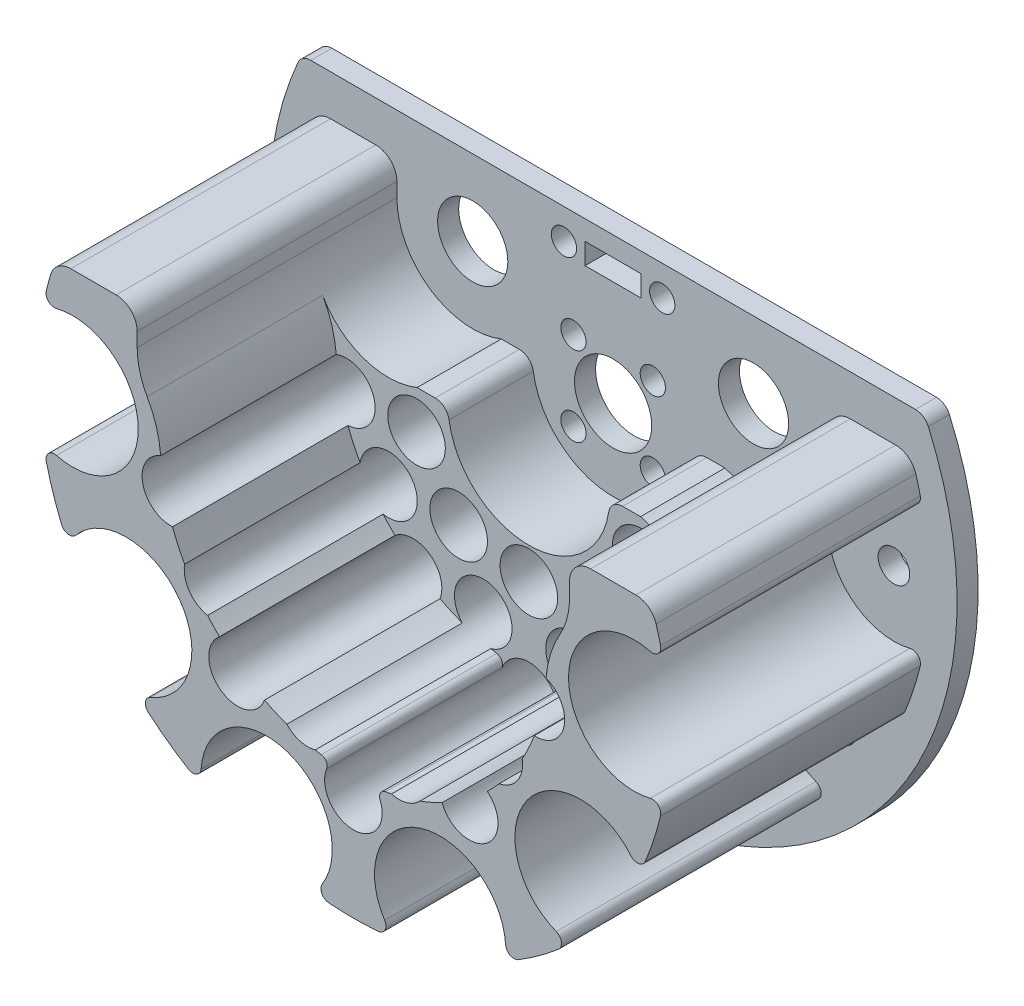
SolidWorks part; units mm, degrees
ref_plane "前视基准面" through (0, 0, 0) normal (0, 0, 1) x (1, 0, 0)
ref_plane "上视基准面" through (0, 0, 0) normal (0, 1, 0) x (1, 0, 0)
ref_plane "右视基准面" through (0, 0, 0) normal (1, 0, 0) x (0, 0, -1)
ref_plane "基准面4" through (0, 0, 40) normal (0, 0, 1) x (1, 0, 0)
sketch "草图1" plane through (0, 0, 40) normal (0, 0, 1) x (1, 0, 0)
  line L0 (-30.8, 160) -> (-30.8, 165)
  line L1 (-30.8, 165) -> (-42.4264, 165)
  line L2 (42.4264, 165) -> (30.8, 165)
  line L3 (30.8, 165) -> (30.8, 160)
  arc A0 (29.3798, 154.6466) -> (27.4312, 148.056) centre (42.4074, 147.2114) ccw
  arc A1 (27.4312, 148.056) -> (-27.4312, 148.056) centre (0, 150) cw
  arc A2 (-27.4312, 148.056) -> (-29.3798, 154.6466) centre (-42.4074, 147.2114) ccw
  arc A3 (-29.3798, 154.6466) -> (-30.8, 160) centre (-20, 160) cw
  arc A4 (-42.4264, 165) -> (-43.756, 160.5075) centre (0, 150) ccw
  arc A5 (-43.756, 160.5075) -> (-42.2947, 159.064) centre (-42.5892, 160.2273) ccw
  arc A6 (-42.2947, 159.064) -> (-42.2947, 140.936) centre (-40, 150) cw
  arc A7 (-42.2947, 140.936) -> (-43.756, 139.4925) centre (-42.5892, 139.7727) ccw
  arc A8 (-43.756, 139.4925) -> (-41.5756, 132.7816) centre (0, 150) ccw
  arc A9 (-41.5756, 132.7816) -> (-39.5448, 132.4728) centre (-40.4669, 133.2408) ccw
  arc A10 (-39.5448, 132.4728) -> (-28.8894, 117.8068) centre (-32.3607, 126.4886) cw
  arc A11 (-28.8894, 117.8068) -> (-29.2232, 115.7801) centre (-28.4439, 116.6926) ccw
  arc A12 (-29.2232, 115.7801) -> (-23.5146, 111.6325) centre (0, 150) ccw
  arc A13 (-23.5146, 111.6325) -> (-21.6902, 112.5763) centre (-22.8876, 112.6557) ccw
  arc A14 (-21.6902, 112.5763) -> (-4.4494, 106.9744) centre (-12.3607, 111.9577) cw
  arc A15 (-4.4494, 106.9744) -> (-3.5281, 105.1385) centre (-3.434, 106.3348) ccw
  arc A16 (-3.5281, 105.1385) -> (3.5281, 105.1385) centre (0, 150) ccw
  arc A17 (3.5281, 105.1385) -> (4.4494, 106.9744) centre (3.434, 106.3348) ccw
  arc A18 (4.4494, 106.9744) -> (21.6902, 112.5763) centre (12.3607, 111.9577) cw
  arc A19 (21.6902, 112.5763) -> (23.5146, 111.6325) centre (22.8876, 112.6557) ccw
  arc A20 (23.5146, 111.6325) -> (29.2232, 115.7801) centre (0, 150) ccw
  arc A21 (29.2232, 115.7801) -> (28.8894, 117.8068) centre (28.4439, 116.6926) ccw
  arc A22 (28.8894, 117.8068) -> (39.5448, 132.4728) centre (32.3607, 126.4886) cw
  arc A23 (39.5448, 132.4728) -> (41.5756, 132.7816) centre (40.4669, 133.2408) ccw
  arc A24 (41.5756, 132.7816) -> (43.756, 139.4925) centre (0, 150) ccw
  arc A25 (43.756, 139.4925) -> (42.2947, 140.936) centre (42.5892, 139.7727) ccw
  arc A26 (42.2947, 140.936) -> (42.2947, 159.064) centre (40, 150) cw
  arc A27 (42.2947, 159.064) -> (43.756, 160.5075) centre (42.5892, 160.2273) ccw
  arc A28 (43.756, 160.5075) -> (42.4264, 165) centre (0, 150) ccw
  arc A29 (30.8, 160) -> (29.3798, 154.6466) centre (20, 160) cw
extrude "凸台-拉伸1" add sketch "草图1" against normal blind 25
sketch "草图2" plane through (0, 0, 15) normal (0, 0, -1) x (-1, 0, 0)
  line L0 (-42.4264, 165) -> (-30.8, 165)
  line L1 (-30.8, 165) -> (-30.8, 160)
  line L2 (-15.9208, 150) -> (-11.5, 150)
  line L3 (11.5, 150) -> (15.9208, 150)
  line L4 (30.8, 160) -> (30.8, 165)
  line L5 (30.8, 165) -> (42.4264, 165)
  arc A0 (-21.6902, 112.5763) -> (-23.5146, 111.6325) centre (-22.8876, 112.6557) cw
  arc A1 (-23.5146, 111.6325) -> (-29.2232, 115.7801) centre (0, 150) cw
  arc A2 (-29.2232, 115.7801) -> (-28.8894, 117.8068) centre (-28.4439, 116.6926) cw
  arc A3 (-28.8894, 117.8068) -> (-39.5448, 132.4728) centre (-32.3607, 126.4886) ccw
  arc A4 (-39.5448, 132.4728) -> (-41.5756, 132.7816) centre (-40.4669, 133.2408) cw
  arc A5 (-41.5756, 132.7816) -> (-43.756, 139.4925) centre (0, 150) cw
  arc A6 (-43.756, 139.4925) -> (-42.2947, 140.936) centre (-42.5892, 139.7727) cw
  arc A7 (-42.2947, 140.936) -> (-42.2947, 159.064) centre (-40, 150) ccw
  arc A8 (-42.2947, 159.064) -> (-43.756, 160.5075) centre (-42.5892, 160.2273) cw
  arc A9 (-43.756, 160.5075) -> (-42.4264, 165) centre (0, 150) cw
  arc A10 (-30.8, 160) -> (-15.9208, 150) centre (-20, 160) ccw
  arc A11 (-11.5, 150) -> (11.5, 150) centre (0, 150) ccw
  arc A12 (15.9208, 150) -> (30.8, 160) centre (20, 160) ccw
  arc A13 (42.4264, 165) -> (43.756, 160.5075) centre (0, 150) cw
  arc A14 (43.756, 160.5075) -> (42.2947, 159.064) centre (42.5892, 160.2273) cw
  arc A15 (42.2947, 159.064) -> (42.2947, 140.936) centre (40, 150) ccw
  arc A16 (42.2947, 140.936) -> (43.756, 139.4925) centre (42.5892, 139.7727) cw
  arc A17 (43.756, 139.4925) -> (41.5756, 132.7816) centre (0, 150) cw
  arc A18 (41.5756, 132.7816) -> (39.5448, 132.4728) centre (40.4669, 133.2408) cw
  arc A19 (39.5448, 132.4728) -> (28.8894, 117.8068) centre (32.3607, 126.4886) ccw
  arc A20 (28.8894, 117.8068) -> (29.2232, 115.7801) centre (28.4439, 116.6926) cw
  arc A21 (29.2232, 115.7801) -> (23.5146, 111.6325) centre (0, 150) cw
  arc A22 (23.5146, 111.6325) -> (21.6902, 112.5763) centre (22.8876, 112.6557) cw
  arc A23 (21.6902, 112.5763) -> (4.4494, 106.9744) centre (12.3607, 111.9577) ccw
  arc A24 (4.4494, 106.9744) -> (3.5281, 105.1385) centre (3.434, 106.3348) cw
  arc A25 (3.5281, 105.1385) -> (-3.5281, 105.1385) centre (0, 150) cw
  arc A26 (-3.5281, 105.1385) -> (-4.4494, 106.9744) centre (-3.434, 106.3348) cw
  arc A27 (-4.4494, 106.9744) -> (-21.6902, 112.5763) centre (-12.3607, 111.9577) ccw
extrude "凸台-拉伸2" add sketch "草图2" along normal blind 12
ref_plane "基准面5" through (0, 0, 3) normal (0, 0, 1) x (1, 0, 0)
sketch "草图3" plane through (0, 0, 3) normal (0, 0, 1) x (1, 0, 0)
  line L0 (44.3662, 170.8) -> (-44.3662, 170.8)
  arc A0 (-44.3662, 170.8) -> (44.3662, 170.8) centre (0, 150) ccw
extrude "凸台-拉伸3" add sketch "草图3" against normal blind 3
sketch "草图4" plane through (0, 0, 0) normal (0, 0, -1) x (-1, 0, 0)
  line L0 (-4, 168) -> (-4, 165)
  line L1 (-4, 165) -> (4, 165)
  line L2 (4, 165) -> (4, 168)
  line L3 (4, 168) -> (-4, 168)
extrude "切除-拉伸1" cut sketch "草图4" against normal through all
ref_plane "基准面6" through (0, 144.5, 0) normal (0, 1, 0) x (1, 0, 0)
sketch "草图5" plane through (0, 144.5, 0) normal (0, 1, 0) x (1, 0, 0)
  line L0 (30.1, -1) -> (26, -1)
  line L1 (26, -1) -> (26, -40)
  line L2 (26, -40) -> (30.1, -40)
  line L3 (30.1, -40) -> (30.1, -1)
  line L4 (26, -1) -> (26, -40) construction
revolve "切除-旋转1" cut sketch "草图5" angle 360 about L4
ref_plane "基准面7" through (0, 136, 0) normal (0, 1, 0) x (1, 0, 0)
sketch "草图6" plane through (0, 136, 0) normal (0, 1, 0) x (1, 0, 0)
  line L0 (24.1, -1) -> (20, -1)
  line L1 (20, -1) -> (20, -40)
  line L2 (20, -40) -> (24.1, -40)
  line L3 (24.1, -40) -> (24.1, -1)
  line L4 (20, -1) -> (20, -40) construction
revolve "切除-旋转2" cut sketch "草图6" angle 360 about L4
ref_plane "基准面8" through (0, 127, 0) normal (0, 1, 0) x (1, 0, 0)
sketch "草图7" plane through (0, 127, 0) normal (0, 1, 0) x (1, 0, 0)
  line L0 (10.6, -1) -> (6.5, -1)
  line L1 (6.5, -1) -> (6.5, -40)
  line L2 (6.5, -40) -> (10.6, -40)
  line L3 (10.6, -40) -> (10.6, -1)
  line L4 (6.5, -1) -> (6.5, -40) construction
revolve "切除-旋转3" cut sketch "草图7" angle 360 about L4
sketch "草图8" plane through (0, 127, 0) normal (0, 1, 0) x (1, 0, 0)
  line L0 (-2.4, -1) -> (-6.5, -1)
  line L1 (-6.5, -1) -> (-6.5, -40)
  line L2 (-6.5, -40) -> (-2.4, -40)
  line L3 (-2.4, -40) -> (-2.4, -1)
  line L4 (-6.5, -1) -> (-6.5, -40) construction
revolve "切除-旋转4" cut sketch "草图8" angle 360 about L4
sketch "草图9" plane through (0, 136, 0) normal (0, 1, 0) x (1, 0, 0)
  line L0 (-15.9, -1) -> (-20, -1)
  line L1 (-20, -1) -> (-20, -40)
  line L2 (-20, -40) -> (-15.9, -40)
  line L3 (-15.9, -40) -> (-15.9, -1)
  line L4 (-20, -1) -> (-20, -40) construction
revolve "切除-旋转5" cut sketch "草图9" angle 360 about L4
sketch "草图10" plane through (0, 144.5, 0) normal (0, 1, 0) x (1, 0, 0)
  line L0 (-21.9, -1) -> (-26, -1)
  line L1 (-26, -1) -> (-26, -40)
  line L2 (-26, -40) -> (-21.9, -40)
  line L3 (-21.9, -40) -> (-21.9, -1)
  line L4 (-26, -1) -> (-26, -40) construction
revolve "切除-旋转6" cut sketch "草图10" angle 360 about L4
hole_wizard "Ø8.2 (8.2) 直径孔1" positions "草图12" profile "草图11" hole size "Ø8.2" standard "ANSI Metric"
sketch "草图12" plane through (0, 0, 40) normal (0, 0, 1) x (1, 0, 0)
  point P0 (-16.5, 127)
  point P1 (16.5, 127)
sketch "草图11" plane through (-16.5, 127, 40) normal (1, 0, 0) x (0, -1, 0)
  line L0 (0, 0) -> (0, 39)
  line L1 (0, 39) -> (4.1, 39)
  line L2 (4.1, 39) -> (4.1, 0)
  line L5 (4.1, 0) -> (0, 0)
  line L10 (0, 39) -> (-4.1, 39) construction
  line L11 (0, -6.35) -> (0, 107.95) construction
  dimension "孔直径" = 8.2
  dimension "孔深度" = 39
  dimension "导头角度" = 180
hole_wizard "Ø8.2 (8.2) 直径孔2" positions "草图14" profile "草图13" hole size "Ø8.2" standard "ANSI Metric"
sketch "草图14" plane through (0, 0, 15) normal (0, 0, 1) x (1, 0, 0)
  point P0 (0, 134)
  point P1 (10, 136)
  point P2 (16, 144.5)
  point P3 (-10, 136)
  point P4 (-16, 144.5)
sketch "草图13" plane through (0, 134, 15) normal (1, 0, 0) x (0, -1, 0)
  line L0 (0, 0) -> (0, 14)
  line L1 (0, 14) -> (4.1, 14)
  line L2 (4.1, 14) -> (4.1, 0)
  line L5 (4.1, 0) -> (0, 0)
  line L10 (0, 14) -> (-4.1, 14) construction
  line L11 (0, -6.35) -> (0, 107.95) construction
  dimension "孔直径" = 8.2
  dimension "孔深度" = 14
  dimension "导头角度" = 180
hole_wizard "Ø8.2 (8.2) 直径孔3" positions "草图16" profile "草图15" hole size "Ø8.2" standard "ANSI Metric"
sketch "草图16" plane through (0, 0, 0) normal (0, 0, -1) x (-1, 0, 0)
  point P0 (0, 120)
sketch "草图15" plane through (0, 120, 0) normal (1, 0, 0) x (0, 1, 0)
  line L0 (0, 0) -> (0, 40)
  line L1 (0, 40) -> (4.1, 40)
  line L2 (4.1, 40) -> (4.1, 0)
  line L5 (4.1, 0) -> (0, 0)
  line L11 (0, -6.35) -> (0, 107.95) construction
  dimension "通孔孔直径" = 8.2
  dimension "通孔孔深度" = 40
hole_wizard "Ø4.5 (4.5) 直径孔1" positions "草图18" profile "草图17" hole size "Ø4.5" standard "ANSI Metric"
sketch "草图18" plane through (0, 0, 0) normal (0, 0, -1) x (-1, 0, 0)
  point P0 (-40, 150)
  point P1 (-32.3607, 126.4886)
  point P2 (-12.3607, 111.9577)
  point P3 (12.3607, 111.9577)
  point P4 (32.3607, 126.4886)
  point P5 (40, 150)
sketch "草图17" plane through (40, 150, 0) normal (1, 0, 0) x (0, 1, 0)
  line L0 (0, 0) -> (0, 40)
  line L1 (0, 40) -> (2.25, 40)
  line L2 (2.25, 40) -> (2.25, 0)
  line L5 (2.25, 0) -> (0, 0)
  line L11 (0, -6.35) -> (0, 107.95) construction
  dimension "通孔孔直径" = 4.5
  dimension "通孔孔深度" = 40
hole_wizard "Ø11.0 (11) 直径孔1" positions "草图20" profile "草图19" hole size "Ø11.0" standard "ANSI Metric"
sketch "草图20" plane through (0, 0, 0) normal (0, 0, -1) x (-1, 0, 0)
  point P0 (0, 150)
sketch "草图19" plane through (0, 150, 0) normal (1, 0, 0) x (0, 1, 0)
  line L0 (0, 0) -> (0, 40)
  line L1 (0, 40) -> (5.5, 40)
  line L2 (5.5, 40) -> (5.5, 0)
  line L5 (5.5, 0) -> (0, 0)
  line L11 (0, -6.35) -> (0, 107.95) construction
  dimension "通孔孔直径" = 11
  dimension "通孔孔深度" = 40
hole_wizard "Ø10.0 (10) 直径孔1" positions "草图22" profile "草图21" hole size "Ø10.0" standard "ANSI Metric"
sketch "草图22" plane through (0, 0, 0) normal (0, 0, -1) x (-1, 0, 0)
  point P0 (20, 160)
  point P1 (-20, 160)
sketch "草图21" plane through (-20, 160, 0) normal (1, 0, 0) x (0, 1, 0)
  line L0 (0, 0) -> (0, 40)
  line L1 (0, 40) -> (5, 40)
  line L2 (5, 40) -> (5, 0)
  line L5 (5, 0) -> (0, 0)
  line L11 (0, -6.35) -> (0, 107.95) construction
  dimension "通孔孔直径" = 10
  dimension "通孔孔深度" = 40
hole_wizard "Ø3.6 (3.6) 直径孔1" positions "草图24" profile "草图23" hole size "Ø3.6" standard "ANSI Metric"
sketch "草图24" plane through (0, 0, 0) normal (0, 0, -1) x (-1, 0, 0)
  point P0 (5.6569, 155.6569)
  point P1 (-7, 166.5)
  point P2 (7, 166.5)
  point P3 (5.6569, 144.3431)
  point P4 (-5.6569, 144.3431)
  point P5 (-5.6569, 155.6569)
sketch "草图23" plane through (-5.6569, 155.6569, 0) normal (1, 0, 0) x (0, 1, 0)
  line L0 (0, 0) -> (0, 40)
  line L1 (0, 40) -> (1.8, 40)
  line L2 (1.8, 40) -> (1.8, 0)
  line L5 (1.8, 0) -> (0, 0)
  line L11 (0, -6.35) -> (0, 107.95) construction
  dimension "通孔孔直径" = 3.6
  dimension "通孔孔深度" = 40
fillet "圆角1" radius 1 2 edges at (3.1063, 122.676, 27.5) (-3.1063, 122.676, 27.5)
fillet "圆角2" radius 2 4 edges at (44.3662, 170.8, 1.5) (-44.3662, 170.8, 1.5) (-11.5, 150, 9) (11.5, 150, 9)
fillet "圆角3" radius 3 4 edges at (42.4264, 165, 21.5) (-30.8, 165, 21.5) (30.8, 165, 21.5) (-42.4264, 165, 21.5)
